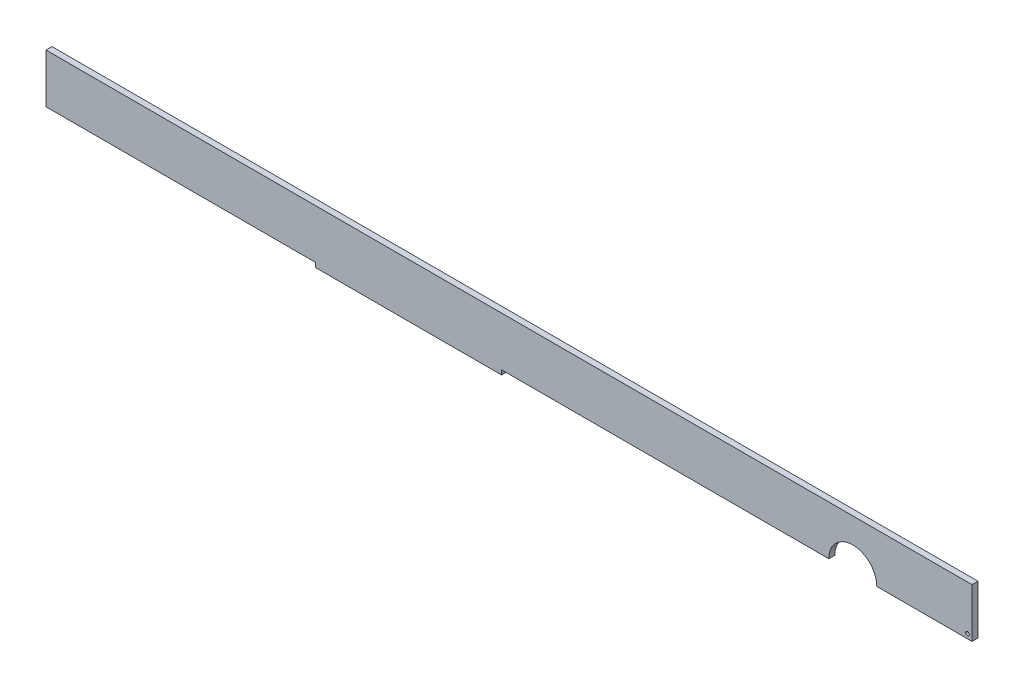
SolidWorks part; units mm, degrees
ref_plane "Płaszczyzna przednia" through (0, 0, 0) normal (0, 0, 1) x (1, 0, 0)
ref_plane "Płaszczyzna górna" through (0, 0, 0) normal (0, 1, 0) x (1, 0, 0)
ref_plane "Płaszczyzna prawa" through (0, 0, 0) normal (1, 0, 0) x (0, 0, -1)
sketch "Szkic1" plane through (0, 0, 0) normal (0, 0, 1) x (1, 0, 0)
  line L1 (-111, 8.2) -> (188, 8.2)
  line L4 (188, 8.2) -> (188, -8.2)
  line L5 (-121, 8.2) -> (-121, -8.2) construction
  line L6 (-121, 8.2) -> (-121, -8.2)
  line L8 (31, -9.7) -> (-31, -9.7)
  line L9 (-31, -8.2) -> (-111, -8.2)
  line L10 (-31, -8.2) -> (-31, -9.7)
  line L11 (31, -8.2) -> (31, -9.7)
  line L12 (31, -8.2) -> (188, -8.2)
  line L13 (-111, 8.2) -> (-121, 8.2)
  line L14 (-111, -8.2) -> (-121, -8.2)
  point P0 (0, 0)
  dimension "D1" = 31
  dimension "D2" = 188
  dimension "D3" = 31
  dimension "D4" = 9.7
extrude "Dodanie-wyciągnięcie1" add sketch "Szkic1" along normal blind 2
sketch "Szkic2" plane through (0, 0, 0) normal (0, 0, -1) x (-1, 0, 0)
  line L0 (-31, -8.2) -> (-188, -8.2) construction
  line L1 (-188, -8.2) -> (-188, 8.2) construction
  circle A0 centre (-186.5, -6.7) radius 0.6
  circle A1 centre (-186.5, 11.2) radius 0.6
  circle A2 centre (186.5, 11.2) radius 0.6
  circle A3 centre (186.5, -11.2) radius 0.6
  circle A4 centre (-148.2207, -8.2) radius 8
  point P9 (-148.2207, -4.2376)
  point P13 (-148.2207, -8.2)
  dimension "D2" = 1.5
  dimension "D1" = 1.5
extrude "Wytnij-wyciągnięcie1" cut sketch "Szkic2" against normal blind 2
